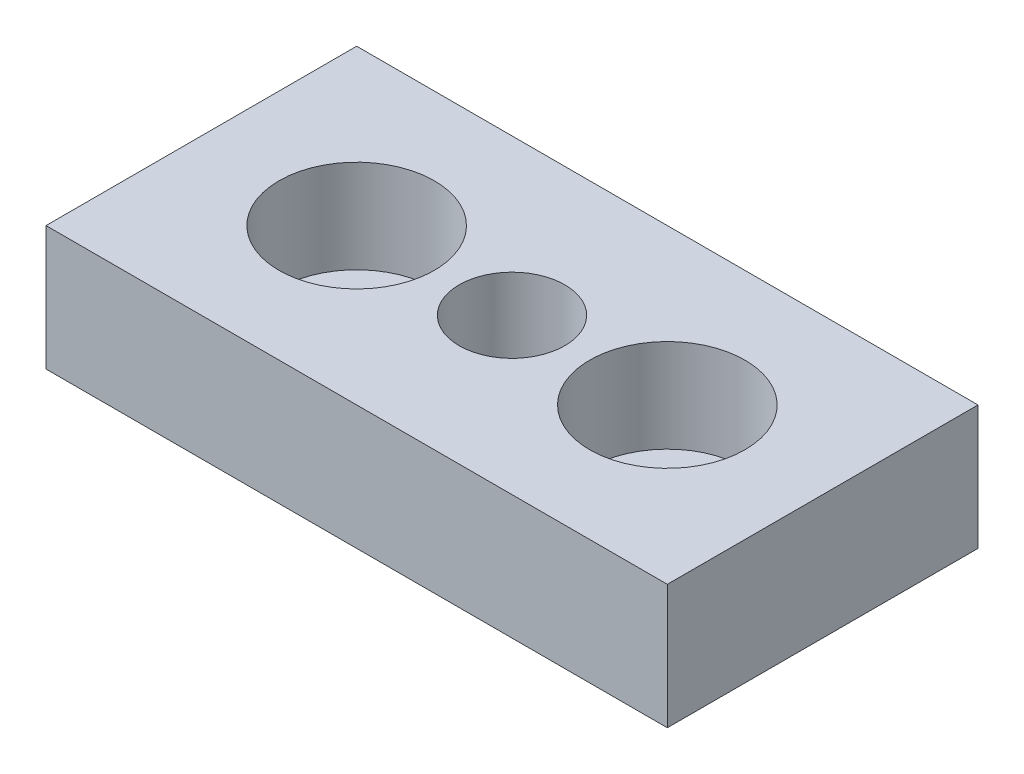
SolidWorks part; units mm, degrees
material "Алюминиевый сплав"
ref_plane "Спереди" through (0, 0, 0) normal (0, 0, 1) x (1, 0, 0)
ref_plane "Сверху" through (0, 0, 0) normal (0, 1, 0) x (1, 0, 0)
ref_plane "Справа" through (0, 0, 0) normal (1, 0, 0) x (0, 0, -1)
sketch "Эскиз1" plane through (0, 0, 0) normal (0, 1, 0) x (1, 0, 0)
  line L1 (-30, -15) -> (30, -15)
  line L2 (-30, -15) -> (-30, 15)
  line L3 (-30, 15) -> (30, 15)
  line L4 (30, -15) -> (30, 15)
  line L5 (-30, -15) -> (30, 15) construction
  line L6 (-30, 15) -> (30, -15) construction
  point P0 (0, 0)
  dimension "D1" = 60
  dimension "D2" = 30
extrude "Бобышка-Вытянуть1" add sketch "Эскиз1" along normal blind 12
sketch "Эскиз2" plane through (0, 0, 0) normal (0, 0, 1) x (1, 0, 0)
  line L0 (0, 0) -> (0, 12) construction
  line L1 (-30, 0) -> (30, 0) construction
  line L2 (-30, 12) -> (30, 12) construction
  line L3 (-22.5, 12) -> (-22.5, 3)
  line L4 (-22.5, 3) -> (-19.5, 3)
  line L5 (-19.5, 3) -> (-19.5, 0)
  line L6 (-19.5, 0) -> (-15, 0)
  line L7 (-15, 0) -> (-15, 12) construction
  line L8 (-15, 12) -> (-22.5, 12)
  line L9 (-15, 12) -> (-15, 0)
  dimension "D1" = 9
  dimension "D2" = 3
  dimension "D3" = 15
  dimension "D4" = 30
revolve "Вырез-Повернуть1" cut sketch "Эскиз2" angle 360 about L9
mirror "Зеркальное отражение1" about plane through (0, 0, 0) normal (1, 0, 0) of "Вырез-Повернуть1"
hole_wizard "Отверстие обработанное метчиком M121" positions "Эскиз3" profile "Эскиз5" tap size "M12" standard "ISO" end condition up to next
sketch "Эскиз3" plane through (0, 12, 0) normal (0, 1, 0) x (1, 0, 0)
  point P0 (0, 0)
sketch "Эскиз5" plane through (0, 12, 0) normal (1, 0, 0) x (0, 0, 1)
  line L0 (0, 0) -> (0, 12)
  line L1 (0, 12) -> (5.1, 12)
  line L2 (5.1, 12) -> (5.1, 0)
  line L5 (5.1, 0) -> (0, 0)
  line L11 (0, -6.35) -> (0, 107.95) construction
  dimension "Диаметр проходного сверла" = 10.2
  dimension "Глубина проходного сверла" = 12
cosmetic thread "Отверстие резьбы1" parameters "D2"=12
